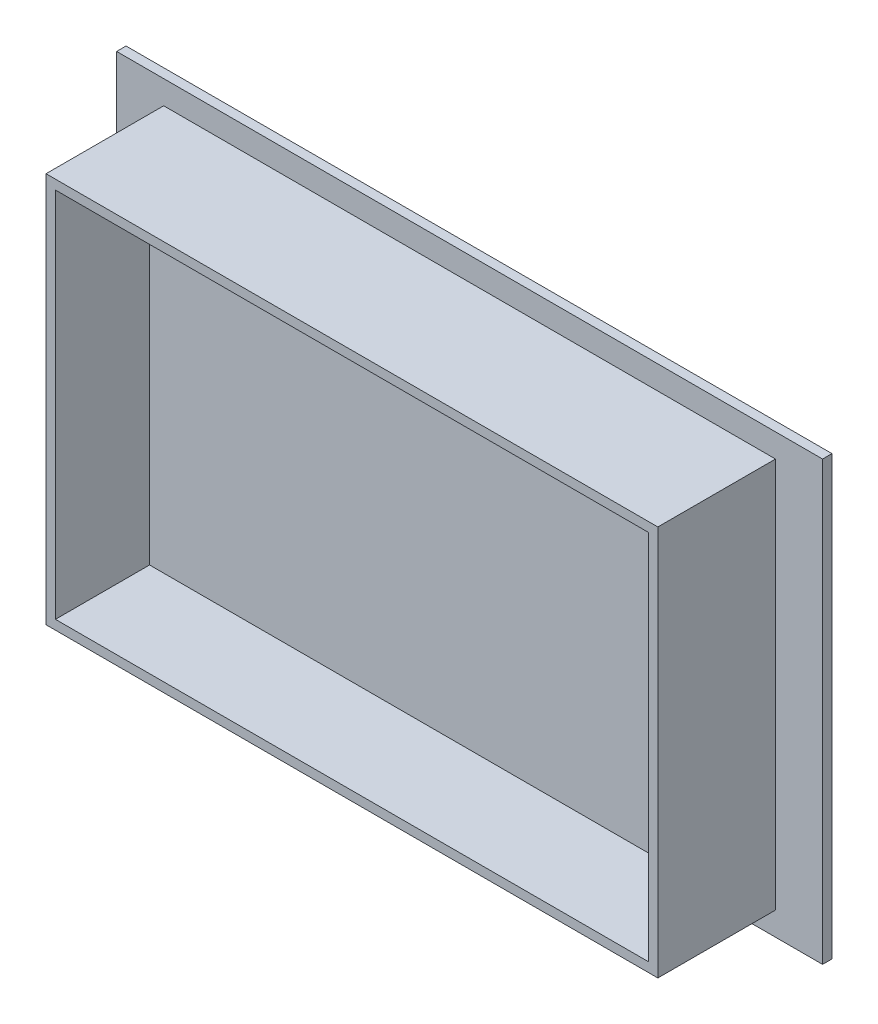
SolidWorks part; units mm, degrees
material "2014 合金"
ref_plane "前视基准面" through (0, 0, 0) normal (0, 0, 1) x (1, 0, 0)
ref_plane "上视基准面" through (0, 0, 0) normal (0, 1, 0) x (1, 0, 0)
ref_plane "右视基准面" through (0, 0, 0) normal (1, 0, 0) x (0, 0, -1)
other "Configuration Table"
sketch "草图1" plane through (0, 0, 0) normal (0, 0, 1) x (1, 0, 0)
  line L1 (-66.2134, 39.5263) -> (83.7866, 39.5263)
  line L2 (-66.2134, 39.5263) -> (-66.2134, -53.4737)
  line L3 (-66.2134, -53.4737) -> (83.7866, -53.4737)
  line L4 (83.7866, 39.5263) -> (83.7866, -53.4737)
  dimension "D1" = 150
  dimension "D2" = 93
extrude "凸台-拉伸2" add sketch "草图1" along normal blind 2
sketch "草图2" plane through (0, 0, 2) normal (0, 0, 1) x (1, 0, 0)
  line L0 (-66.2134, 39.5263) -> (-66.2134, -53.4737) construction
  line L1 (-56.2134, 34.5263) -> (73.7866, 34.5263)
  line L2 (-56.2134, 34.5263) -> (-56.2134, -48.4737)
  line L3 (-56.2134, -48.4737) -> (73.7866, -48.4737)
  line L4 (73.7866, 34.5263) -> (73.7866, -48.4737)
  line L5 (83.7866, 39.5263) -> (-66.2134, 39.5263) construction
  dimension "D1" = 130
  dimension "D2" = 83
  dimension "D3" = 10
  dimension "D4" = 5
extrude "凸台-拉伸3" add sketch "草图2" along normal blind 25
sketch "草图3" plane through (0, 0, 0) normal (0, 0, -1) x (-1, 0, 0)
  line L0 (-83.7866, 39.5263) -> (66.2134, 39.5263) construction
  line L1 (-71.7866, 32.5263) -> (54.2134, 32.5263)
  line L2 (-71.7866, 32.5263) -> (-71.7866, -46.4737)
  line L3 (-71.7866, -46.4737) -> (54.2134, -46.4737)
  line L4 (54.2134, 32.5263) -> (54.2134, -46.4737)
  line L5 (-83.7866, -53.4737) -> (-83.7866, 39.5263) construction
  dimension "D1" = 7
  dimension "D2" = 12
  dimension "D3" = 126
  dimension "D4" = 79
extrude "切除-拉伸1" cut sketch "草图3" against normal blind 2
sketch "草图4" plane through (0, 0, 27) normal (0, 0, 1) x (1, 0, 0)
  line L0 (-56.2134, 34.5263) -> (-56.2134, -48.4737) construction
  line L1 (-54.2134, 32.5263) -> (71.7866, 32.5263)
  line L2 (-54.2134, 32.5263) -> (-54.2134, -46.4737)
  line L3 (-54.2134, -46.4737) -> (71.7866, -46.4737)
  line L4 (71.7866, 32.5263) -> (71.7866, -46.4737)
  line L5 (73.7866, 34.5263) -> (-56.2134, 34.5263) construction
  dimension "D1" = 126
  dimension "D2" = 79
  dimension "D3" = 2
  dimension "D4" = 2
extrude "切除-拉伸2" cut sketch "草图4" against normal blind 20
